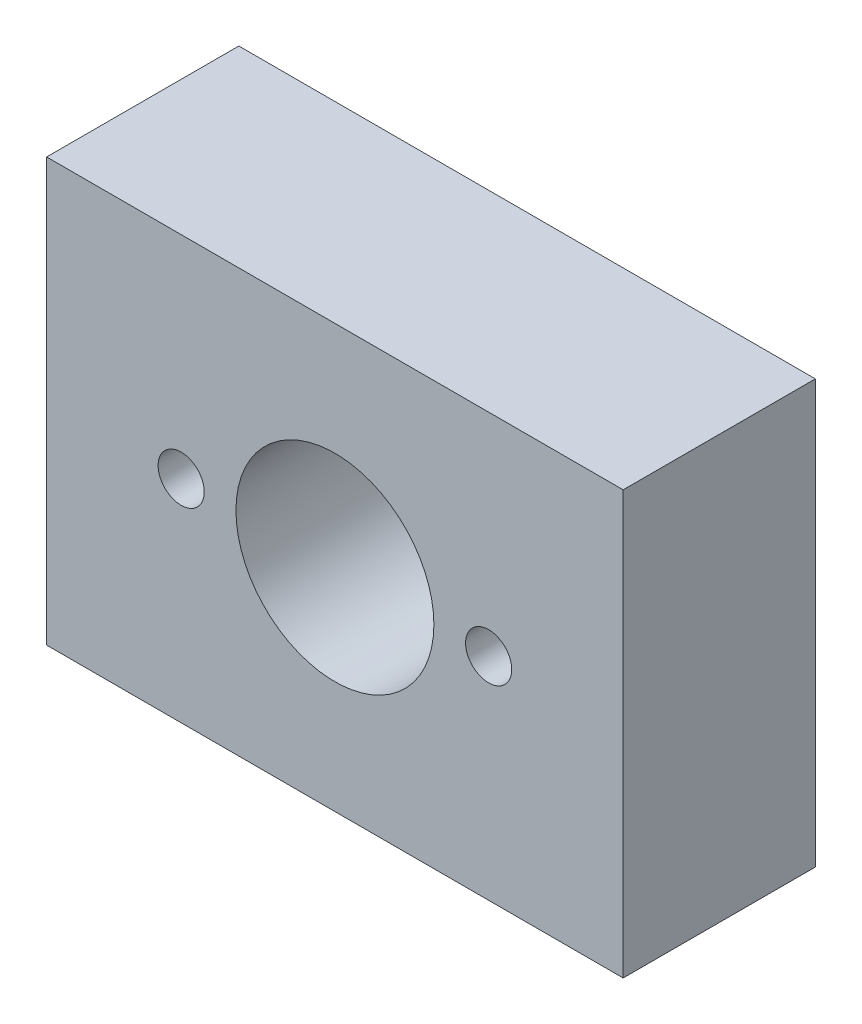
SolidWorks part; units mm, degrees
ref_plane "Front Plane" through (0, 0, 0) normal (0, 0, 1) x (1, 0, 0)
ref_plane "Top Plane" through (0, 0, 0) normal (0, 1, 0) x (1, 0, 0)
ref_plane "Right Plane" through (0, 0, 0) normal (1, 0, 0) x (0, 0, -1)
sketch "Sketch1" plane through (0, 0, 0) normal (0, 0, 1) x (1, 0, 0)
  line L1 (15, -11) -> (-15, -11)
  line L2 (15, -11) -> (15, 11)
  line L3 (15, 11) -> (-15, 11)
  line L4 (-15, -11) -> (-15, 11)
  circle A0 centre (0, 0) radius 11 construction
  circle A1 centre (0, 0) radius 5.15
  point P0 (0, 0)
  point P9 (-15, 0)
  point P10 (0, 11)
  point P16 (0, 0)
  dimension "D1" = 22
  dimension "D4" = 10.3
  dimension "D2" = 11
  dimension "D3" = 30
extrude "Boss-Extrude1" add sketch "Sketch1" along normal blind 10
sketch "Sketch2" plane through (0, -11, 0) normal (0, -1, 0) x (1, 0, 0)
  line L0 (0, 10) -> (0, 0) construction
  line L1 (-15, 10) -> (15, 10) construction
  circle A0 centre (-11, 5) radius 2
  circle A1 centre (11, 5) radius 2
  point P9 (0, 0)
  point P10 (0, 5)
  dimension "D2" = 4
  dimension "D1" = 22
extrude "Cut-Extrude1" cut sketch "Sketch2" against normal blind 10
sketch "Sketch7" plane through (0, 0, 10) normal (0, 0, 1) x (1, 0, 0)
  line L0 (0, 11) -> (0, 0) construction
  line L1 (15, 11) -> (-15, 11) construction
  circle A0 centre (-8, 0) radius 1.2
  circle A1 centre (8, 0) radius 1.2
  point P9 (0, 0)
  dimension "D1" = 2.4
  dimension "D2" = 16
extrude "Cut-Extrude2" cut sketch "Sketch7" against normal through all
